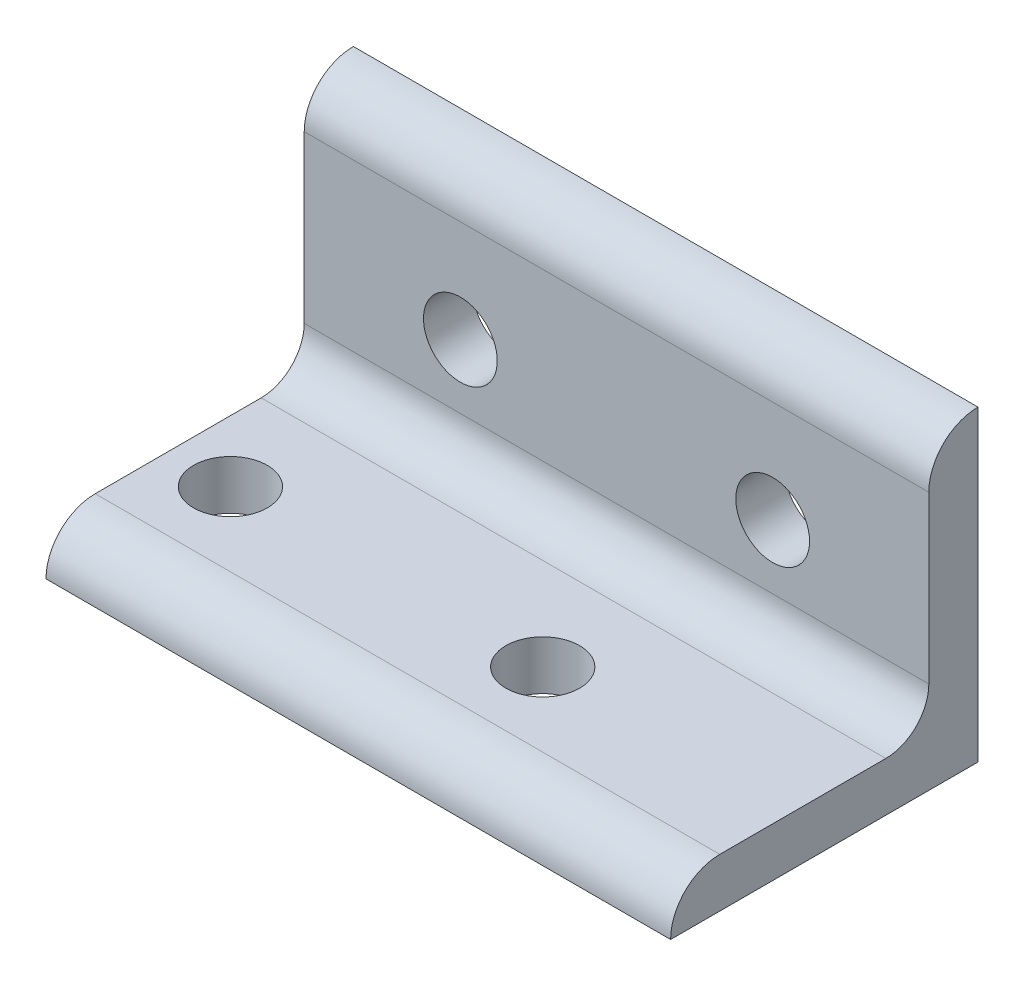
SolidWorks part; units mm, degrees
ref_plane "Front Plane" through (0, 0, 0) normal (0, 0, 1) x (1, 0, 0)
ref_plane "Top Plane" through (0, 0, 0) normal (0, 1, 0) x (1, 0, 0)
ref_plane "Right Plane" through (0, 0, 0) normal (1, 0, 0) x (0, 0, -1)
sketch "Sketch1" plane through (0, 0, 0) normal (0, 0, 1) x (1, 0, 0)
  line L0 (-30.5967, 0) -> (20.2033, 0)
  dimension "D1" = 50.8
other "Structural Member1"
ref_plane "Plane1" through (-30.5967, 0, 0) normal (1, 0, 0) x (0, 1, 0)
sketch "Sketch12" plane through (-30.5967, 0, 0) normal (1, 0, 0) x (0, 1, 0)
  line L0 (0, 0) -> (0, 25)
  line L1 (0, 12.5) -> (4, 12.5) construction
  line L2 (4, 21) -> (4, 7.5)
  line L3 (7.5, 4) -> (21, 4)
  line L4 (12.5, 4) -> (12.5, 0) construction
  line L5 (25, 0) -> (0, 0)
  arc A0 (25, 0) -> (21, 4) centre (21, 0) ccw
  arc A1 (0, 25) -> (4, 21) centre (0, 21) cw
  arc A2 (7.5, 4) -> (4, 7.5) centre (7.5, 7.5) cw
  point P10 (12.5, 0)
  point P14 (0, 12.5)
  point P15 (4, 12.5)
  point P16 (12.5, 4)
  point P17 (4, 25)
  point P18 (25, 4)
  point P21 (0, 0)
  dimension "D2" = 4
  dimension "D3" = 25
  dimension "Radius_1" = 3.5
  dimension "D1" = 4
sketch "Sketch13" plane through (0, 0, 4) normal (0, 0, 1) x (1, 0, 0)
  line L0 (20.2033, 21) -> (-30.5967, 21) construction
  circle A0 centre (-17.8967, 12.7) radius 3
  circle A1 centre (7.5033, 12.7) radius 3
  point P4 (-5.1967, 21)
  dimension "D1" = 6
  dimension "D2" = 25.4
  dimension "D3" = 12.7
  dimension "D4" = 12.7
extrude "Cut-Extrude1" cut sketch "Sketch13" against normal through all
sketch "Sketch14" plane through (0, 4, 0) normal (0, 1, 0) x (-1, 0, 0)
  line L0 (-20.2033, 21) -> (30.5967, 21) construction
  line L1 (-20.2033, 25) -> (30.5967, 25) construction
  circle A0 centre (25.5967, 15) radius 3
  circle A1 centre (0.1967, 15) radius 3
  point P7 (5.1967, 21)
  dimension "D1" = 6
  dimension "D2" = 25.4
  dimension "D3" = 5
  dimension "D4" = 10
extrude "Cut-Extrude2" cut sketch "Sketch14" against normal through all
